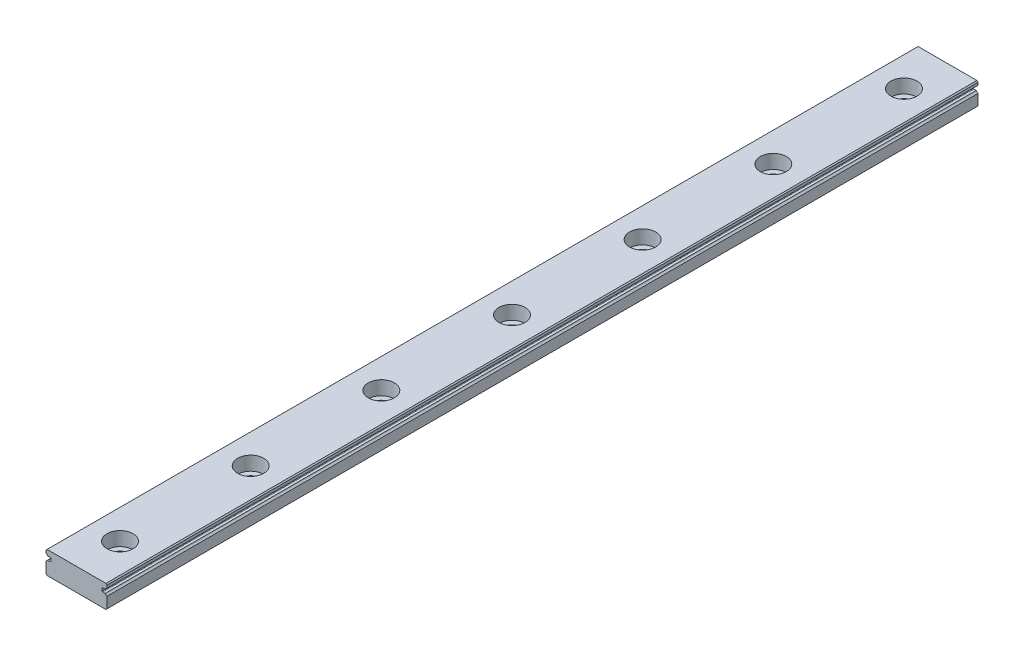
SolidWorks part; units mm, degrees
ref_plane "前视基准面" through (0, 0, 0) normal (0, 0, 1) x (1, 0, 0)
ref_plane "上视基准面" through (0, 0, 0) normal (0, 1, 0) x (1, 0, 0)
ref_plane "右视基准面" through (0, 0, 0) normal (1, 0, 0) x (0, 0, -1)
ref_plane "基准面4" through (0, 3.3, 0) normal (0, 1, 0) x (1, 0, 0)
sketch "草图1" plane through (0, 3.3, 0) normal (0, 1, 0) x (1, 0, 0)
  line L0 (-7, -100) -> (7, -100)
  line L1 (7, -100) -> (7, 100)
  line L2 (7, 100) -> (-7, 100)
  line L3 (-7, 100) -> (-7, -100)
extrude "凸台-拉伸1" add sketch "草图1" against normal blind 5.2
sketch "草图2" plane through (0, 0, -100) normal (0, 0, -1) x (-1, 0, 0)
  line L0 (7, 1.23) -> (7, 2.4413)
  line L1 (6.5936, 2.07) -> (5.8936, 2.07)
  line L2 (5.8936, 2.07) -> (5.8936, 1.23)
  line L3 (5.8936, 1.23) -> (7, 1.23)
  arc A0 (7, 2.4413) -> (6.5936, 2.07) centre (7.35, 1.65) ccw
extrude "切除-拉伸1" cut sketch "草图2" against normal through all
sketch "草图3" plane through (0, 0, -100) normal (0, 0, -1) x (-1, 0, 0)
  line L0 (7, 0.8587) -> (7, 1.23)
  line L1 (7, 1.23) -> (6.5936, 1.23)
  arc A0 (6.5936, 1.23) -> (7, 0.8587) centre (7.35, 1.65) ccw
extrude "切除-拉伸2" cut sketch "草图3" against normal through all
sketch "草图4" plane through (0, 0, -100) normal (0, 0, -1) x (-1, 0, 0)
  line L0 (-7, 2.07) -> (-7, 0.8587)
  line L1 (-6.5936, 1.23) -> (-5.8936, 1.23)
  line L2 (-5.8936, 1.23) -> (-5.8936, 2.07)
  line L3 (-5.8936, 2.07) -> (-7, 2.07)
  arc A0 (-7, 0.8587) -> (-6.5936, 1.23) centre (-7.35, 1.65) ccw
extrude "切除-拉伸3" cut sketch "草图4" against normal through all
sketch "草图5" plane through (0, 0, -100) normal (0, 0, -1) x (-1, 0, 0)
  line L0 (-7, 2.4413) -> (-7, 2.07)
  line L1 (-7, 2.07) -> (-6.5936, 2.07)
  arc A0 (-6.5936, 2.07) -> (-7, 2.4413) centre (-7.35, 1.65) ccw
extrude "切除-拉伸4" cut sketch "草图5" against normal through all
hole_wizard "M3 六角头机械螺钉的柱形沉头孔1" positions "草图7" profile "草图6" counterbore size "M3" standard "ANSI Metric"
sketch "草图7" plane through (0, 3.3, 0) normal (0, 1, 0) x (1, 0, 0)
  point P0 (0, 90)
  point P1 (0, 60)
  point P2 (0, 30)
  point P3 (0, 0)
  point P4 (0, -30)
  point P5 (0, -60)
  point P6 (0, -90)
sketch "草图6" plane through (0, 3.3, -90) normal (1, 0, 0) x (0, 0, 1)
  line L0 (0, 0) -> (0, 5.2)
  line L1 (0, 5.2) -> (1.75, 5.2)
  line L3 (1.75, 5.2) -> (1.75, 3.2)
  line L4 (1.75, 3.2) -> (3, 3.2)
  line L5 (3, 3.2) -> (3, 0)
  line L7 (3, 0) -> (0, 0)
  line L11 (0, -6.35) -> (0, 107.95) construction
  dimension "通孔孔直径" = 3.5
  dimension "通孔孔深度" = 5.2
  dimension "柱形沉头孔直径" = 6
  dimension "柱形沉头孔深度" = 3.2
chamfer "倒角1" distance 0.2475 angle 45 4 edges at (-7, 3.3, 0) (-7, -1.9, 0) (7, 3.3, 0) (7, -1.9, 0)
fillet "圆角1" radius 0.14 4 edges at (-5.8936, 2.07, 0) (5.8936, 2.07, 0) (-5.8936, 1.23, 0) (5.8936, 1.23, 0)
